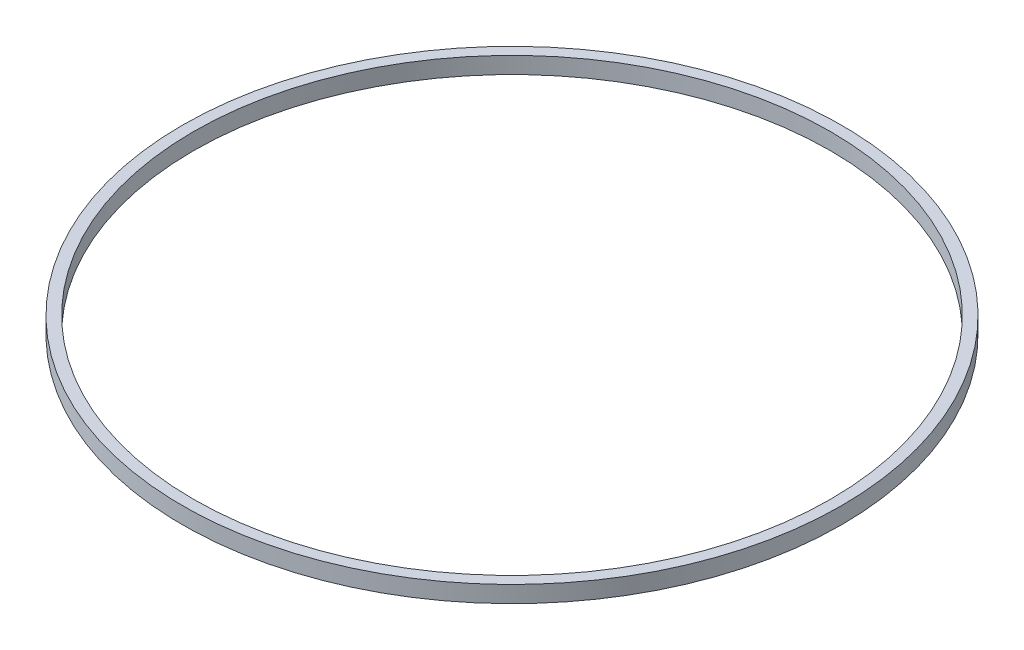
SolidWorks part; units mm, degrees
ref_plane "Plan de face" through (0, 0, 0) normal (0, 0, 1) x (1, 0, 0)
ref_plane "Plan de dessus" through (0, 0, 0) normal (0, 1, 0) x (1, 0, 0)
ref_plane "Plan de droite" through (0, 0, 0) normal (1, 0, 0) x (0, 0, -1)
sketch "Esquisse1" plane through (0, 0, 0) normal (0, 0, 1) x (1, 0, 0)
  line L0 (0, 3) -> (0, 0) construction
  line L1 (0, 0) -> (-57.5, 0) construction
  line L2 (-57.5, 0) -> (-59.5, 0)
  line L3 (-57.5, 0) -> (-57.5, 3)
  line L4 (-57.5, 3) -> (-59.5, 3)
  line L5 (-59.5, 0) -> (-59.5, 3)
  dimension "D1" = 3
  dimension "D2" = 2
  dimension "D3" = 57.5
  dimension "D4" = 3
revolve "Révolution1" add sketch "Esquisse1" angle 360 about L0
